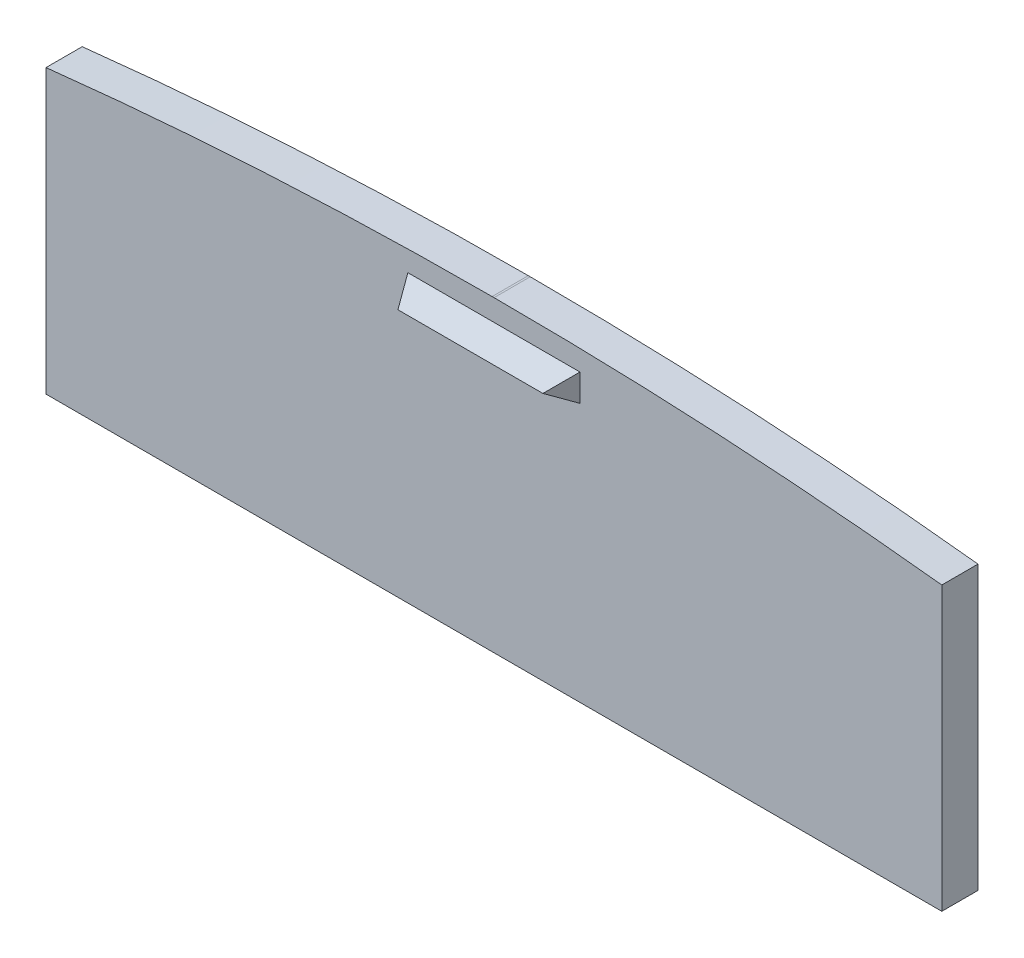
SolidWorks part; units mm, degrees
ref_plane "Plan de face" through (0, 0, 0) normal (0, 0, 1) x (1, 0, 0)
ref_plane "Plan de dessus" through (0, 0, 0) normal (0, 1, 0) x (1, 0, 0)
ref_plane "Plan de droite" through (0, 0, 0) normal (1, 0, 0) x (0, 0, -1)
sketch "Esquisse2" plane through (0, 0, 0) normal (0, 0, 1) x (1, 0, 0)
  line L1 (15.843, 122.6491) -> (114.8672, 122.6491)
  line L2 (15.843, 122.6491) -> (15.843, 156.6491)
  line L3 (15.843, 156.6491) -> (114.8672, 156.6491)
  line L4 (114.8672, 122.6491) -> (114.8672, 156.6491)
  arc A0 (-4.6371, 118.1842) -> (135.3629, 118.1505) centre (65.2643, -290.8864) cw construction
  arc A1 (140.8585, 150.2185) -> (-10.1173, 150.2549) centre (65.2643, -290.8864) ccw
  arc A2 (129.8672, 86.0825) -> (0.843, 86.1136) centre (65.2643, -290.8864) ccw
  arc A3 (129.8672, 86.0825) -> (140.8585, 150.2185) centre (135.3629, 118.1505) ccw
  arc A4 (-10.1173, 150.2549) -> (0.843, 86.1136) centre (-4.6371, 118.1842) ccw
  point P3 (65.3643, 124.1136)
  point P12 (65.3721, 156.6491)
  dimension "D1" = 415
  dimension "D2" = 140
  dimension "D3" = 38
  dimension "D4" = 0.1
  dimension "D5" = 0
  dimension "D6" = 34
  dimension "D7" = 15
  dimension "D8" = 15
extrude "Boss.-Extru.2" add sketch "Esquisse2" along normal blind 4 contours L4 A1 L3 L2 L1
sketch "Esquisse6" plane through (0, 0, 4) normal (0, 0, 1) x (1, 0, 0)
  line L0 (15.843, 122.6491) -> (15.843, 153.912) construction
  line L1 (55.843, 154.2778) -> (74.8672, 154.2778)
  line L2 (55.843, 154.2778) -> (55.843, 151.2778)
  line L3 (55.843, 151.2778) -> (74.8672, 151.2778)
  line L4 (74.8672, 154.2778) -> (74.8672, 151.2778)
  line L5 (114.8672, 122.6491) -> (114.8672, 153.8917) construction
  dimension "D1" = 40
  dimension "D2" = 40
  dimension "D3" = 3
extrude "Boss.-Extru.3" add sketch "Esquisse6" along normal blind 3 draft 30
